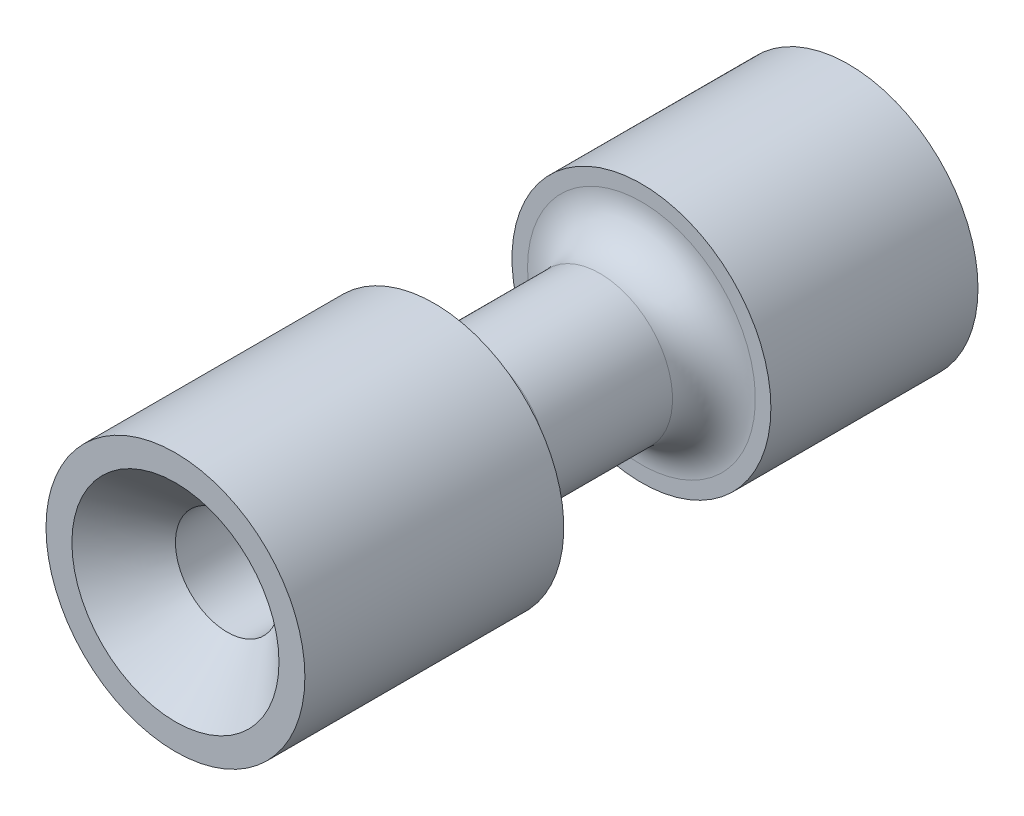
SolidWorks part; units mm, degrees
ref_plane "Front Plane" through (0, 0, 0) normal (0, 0, 1) x (1, 0, 0)
ref_plane "Top Plane" through (0, 0, 0) normal (0, 1, 0) x (1, 0, 0)
ref_plane "Right Plane" through (0, 0, 0) normal (1, 0, 0) x (0, 0, -1)
sketch "Sketch1" plane through (0, 0, 0) normal (0, 0, 1) x (1, 0, 0)
  circle A0 centre (0, 0) radius 2.5
  dimension "D1" = 5
extrude "Boss-Extrude1" add sketch "Sketch1" along normal blind 13
cosmetic thread "Cosmetic Thread2" parameters "D1"=13, "D2"=4.11
sketch "Sketch3" plane through (0, 0, 0) normal (0, 1, 0) x (1, 0, 0)
  line L1 (3.1382, -4) -> (2.2, -4)
  line L2 (3.1382, -4) -> (3.1382, -8)
  line L3 (3.1382, -8) -> (2.2, -8)
  line L4 (1.4, -4.8) -> (1.4, -7.2)
  line L7 (0, 0) -> (0, -16.2401) construction
  line L8 (2.5, 0) -> (-2.5, 0) construction
  arc A0 (1.4, -7.2) -> (2.2, -8) centre (2.2, -7.2) ccw
  arc A1 (2.2, -4) -> (1.4, -4.8) centre (2.2, -4.8) ccw
  dimension "D4" = 0.8
  dimension "D1" = 1.4
  dimension "D2" = 4
  dimension "D3" = 4
revolve "Cut-Revolve1" cut sketch "Sketch3" angle 360 about L7
hole_wizard "Ø2.0 (2) Diameter Hole1" positions "Sketch5" profile "Sketch4" hole size "Ø2.0" standard "Ansi Metric" end condition through all
sketch "Sketch5" plane through (0, 0, 13) normal (0, 0, 1) x (1, 0, 0)
  point P0 (0, 0)
sketch "Sketch4" plane through (0, 0, 13) normal (1, 0, 0) x (0, -1, 0)
  line L0 (0, 0) -> (0, 13)
  line L1 (0, 13) -> (1, 13)
  line L2 (1, 13) -> (1, 0)
  line L5 (1, 0) -> (0, 0)
  line L11 (0, -6.35) -> (0, 107.95) construction
  dimension "Thru Hole Dia." = 2
  dimension "Thru Hole Depth" = 13
sketch "Sketch6" plane through (0, 0, 0) normal (0, 0, -1) x (-1, 0, 0)
  circle A0 centre (0, 0) radius 0.25
  dimension "D1" = 0.5
chamfer "Chamfer2" distance 1 angle 45 1 edges at (1, 0, 13)
